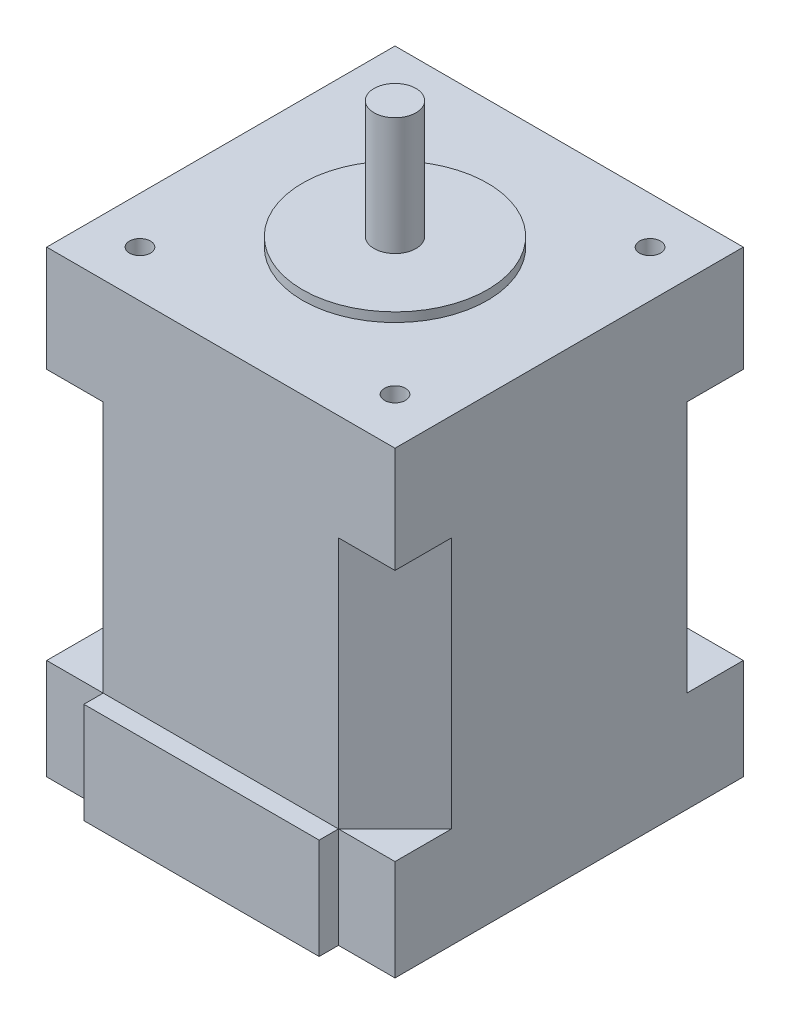
SolidWorks part; units mm, degrees
ref_plane "Front Plane" through (0, 0, 0) normal (0, 0, 1) x (1, 0, 0)
ref_plane "Top Plane" through (0, 0, 0) normal (0, 1, 0) x (1, 0, 0)
ref_plane "Right Plane" through (0, 0, 0) normal (1, 0, 0) x (0, 0, -1)
sketch "Sketch1" plane through (0, 0, 0) normal (0, 1, 0) x (1, 0, 0)
  line L1 (-20.725, 20.725) -> (20.725, 20.725)
  line L2 (-20.725, 20.725) -> (-20.725, -20.725)
  line L3 (-20.725, -20.725) -> (20.725, -20.725)
  line L4 (20.725, 20.725) -> (20.725, -20.725)
  line L5 (-20.725, 20.725) -> (20.725, -20.725) construction
  line L6 (-20.725, -20.725) -> (20.725, 20.725) construction
  point P0 (0, 0)
  dimension "D1" = 41.45
extrude "Boss-Extrude1" add sketch "Sketch1" along normal blind 54.6
sketch "Sketch2" plane through (0, 54.6, 0) normal (0, 1, 0) x (1, 0, 0)
  circle A0 centre (0, 0) radius 11
  dimension "D1" = 22
extrude "Boss-Extrude2" add sketch "Sketch2" along normal blind 1.1
sketch "Sketch3" plane through (0, 55.7, 0) normal (0, 1, 0) x (1, 0, 0)
  circle A0 centre (0, 0) radius 2.5
  dimension "D1" = 5
extrude "Boss-Extrude3" add sketch "Sketch3" along normal blind 14
sketch "Sketch4" plane through (0, 0, 0) normal (0, -1, 0) x (1, 0, 0)
  line L0 (0, 20.725) -> (14, 20.725)
  line L1 (-20.725, 20.725) -> (20.725, 20.725) construction
  line L2 (0, 20.725) -> (-14, 20.725)
  line L3 (-14, 20.725) -> (-14, 23.025)
  line L4 (-14, 23.025) -> (14, 23.025)
  line L5 (14, 23.025) -> (14, 20.725)
  dimension "D1" = 14
  dimension "D2" = 14
  dimension "D3" = 2.3
extrude "Boss-Extrude4" add sketch "Sketch4" against normal blind 12
sketch "Sketch5" plane through (0, 54.6, 0) normal (0, 1, 0) x (1, 0, 0)
  line L0 (20.725, 20.725) -> (-20.725, 20.725) construction
  line L1 (20.725, -20.725) -> (20.725, 20.725) construction
  circle A0 centre (15.175, 15.175) radius 1.25
  dimension "D1" = 2.5
  dimension "D5" = 5.55
  dimension "D6" = 5.55
extrude "Cut-Extrude1" cut sketch "Sketch5" against normal blind 12
mirror "Mirror1" about plane through (0, 0, 0) normal (0, 0, 1) of "Cut-Extrude1"
mirror "Mirror2" about plane through (0, 0, 0) normal (1, 0, 0) of "Mirror1", "Cut-Extrude1"
sketch "Sketch6" plane through (-20.725, 0, 0) normal (-1, 0, 0) x (0, 0, 1)
  line L0 (-20.725, 0) -> (-20.725, 12)
  line L1 (-20.725, 54.6) -> (-20.725, 0) construction
  line L2 (-20.725, 12) -> (20.725, 12)
  dimension "D1" = 12
sketch "Sketch7" plane through (0, 0, -20.725) normal (0, 0, -1) x (-1, 0, 0)
  line L0 (20.725, 12) -> (-20.725, 12)
  line L1 (20.725, 0) -> (20.725, 12) construction
  line L2 (-20.725, 54.6) -> (-20.725, 0) construction
ref_plane "Plane1" through (0, 12, 0) normal (0, 1, 0) x (1, 0, 0)
sketch "Sketch8" plane through (0, 12, 0) normal (0, 1, 0) x (1, 0, 0)
  line L0 (-20.725, 0) -> (-20.725, -14)
  line L1 (-20.725, 20.725) -> (-20.725, -20.725) construction
  line L2 (-20.725, 0) -> (-20.725, 14)
  line L3 (0, 20.725) -> (-14, 20.725)
  line L4 (-20.725, 20.725) -> (20.725, 20.725) construction
  line L5 (0, 20.725) -> (14, 20.725)
  line L6 (-20.725, 14) -> (-20.725, 20.725)
  line L7 (-20.725, 20.725) -> (-14, 20.725)
  line L8 (-14, 20.725) -> (-20.725, 14)
  dimension "D1" = 14
  dimension "D2" = 14
  dimension "D3" = 14
  dimension "D4" = 14
extrude "Cut-Extrude2" cut sketch "Sketch8" along normal blind 30 contours L6 L7 L8
mirror "Mirror3" about plane through (0, 0, 0) normal (1, 0, 0) of "Cut-Extrude2"
mirror "Mirror4" about plane through (0, 0, 0) normal (0, 0, 1) of "Mirror3", "Cut-Extrude2"
sketch "Sketch10" plane through (0, 0, 0) normal (0, -1, 0) x (1, 0, 0)
  circle A0 centre (0, 0) radius 4.45
  dimension "D1" = 8.9
extrude "Cut-Extrude3" cut sketch "Sketch10" against normal blind 6
